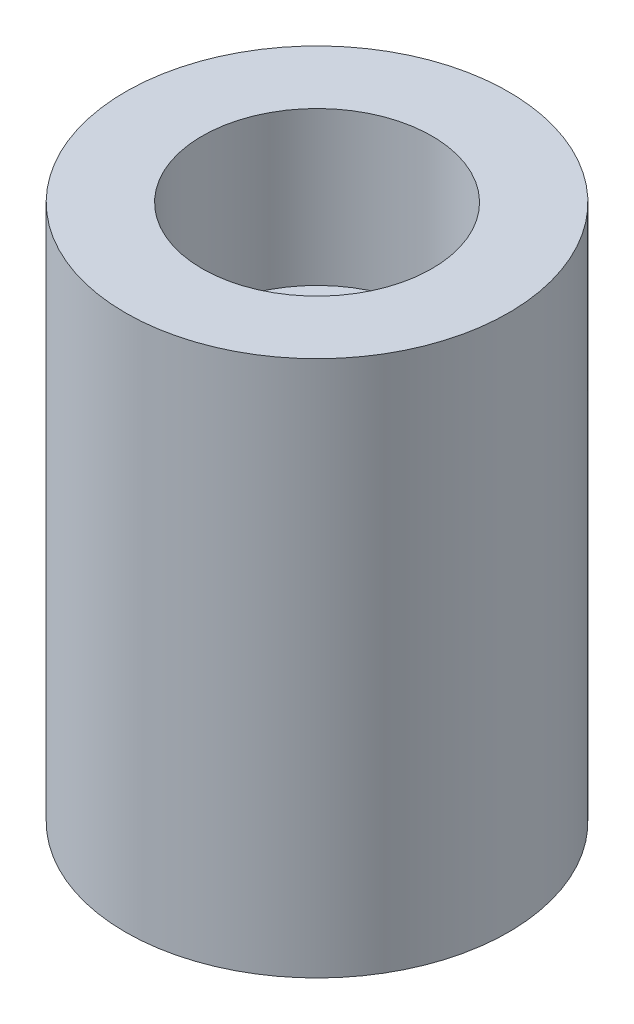
SolidWorks part; units mm, degrees
ref_plane "Front Plane" through (0, 0, 0) normal (0, 0, 1) x (1, 0, 0)
ref_plane "Top Plane" through (0, 0, 0) normal (0, 1, 0) x (1, 0, 0)
ref_plane "Right Plane" through (0, 0, 0) normal (1, 0, 0) x (0, 0, -1)
sketch "Sketch1" plane through (0, 0, 0) normal (0, 1, 0) x (1, 0, 0)
  circle A0 centre (0, 0) radius 50
  dimension "D1" = 100
extrude "Boss-Extrude1" add sketch "Sketch1" along normal blind 140
sketch "Sketch2" plane through (0, 140, 0) normal (0, 1, 0) x (1, 0, 0)
  circle A0 centre (0, 0) radius 30
  dimension "D1" = 60
extrude "Cut-Extrude1" cut sketch "Sketch2" against normal blind 40
sketch "Sketch3" plane through (0, 100, 0) normal (0, 1, 0) x (1, 0, 0)
  circle A0 centre (0, 0) radius 10
  dimension "D1" = 20
extrude "Cut-Extrude2" cut sketch "Sketch3" against normal blind 80
